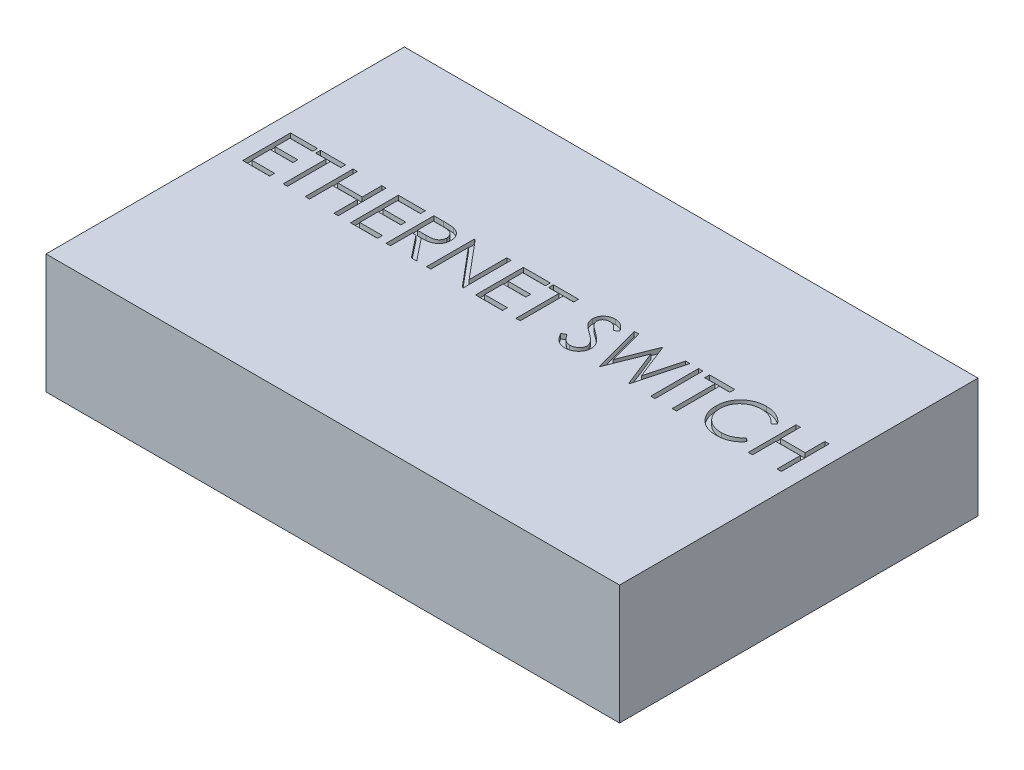
SolidWorks part; units mm, degrees
ref_plane "Front Plane" through (0, 0, 0) normal (0, 0, 1) x (1, 0, 0)
ref_plane "Top Plane" through (0, 0, 0) normal (0, 1, 0) x (1, 0, 0)
ref_plane "Right Plane" through (0, 0, 0) normal (1, 0, 0) x (0, 0, -1)
sketch "Sketch1" plane through (0, 0, 0) normal (0, 1, 0) x (1, 0, 0)
  line L1 (0, 0) -> (120, 0)
  line L2 (0, 0) -> (0, 75)
  line L3 (0, 75) -> (120, 75)
  line L4 (120, 0) -> (120, 75)
  dimension "D1" = 75
  dimension "D2" = 120
extrude "Boss-Extrude1" add sketch "Sketch1" along normal blind 25
sketch "Sketch2" plane through (0, 25, 0) normal (0, 1, 0) x (1, 0, 0)
  line L0 (0, 37.5) -> (120, 37.5) construction
  line L1 (0, 75) -> (0, 0) construction
  line L2 (120, 0) -> (120, 75) construction
  text T0 "ETHERNET SWITCH" font "Century Gothic" height 10
extrude "Cut-Extrude1" cut sketch "Sketch2" against normal blind 1
